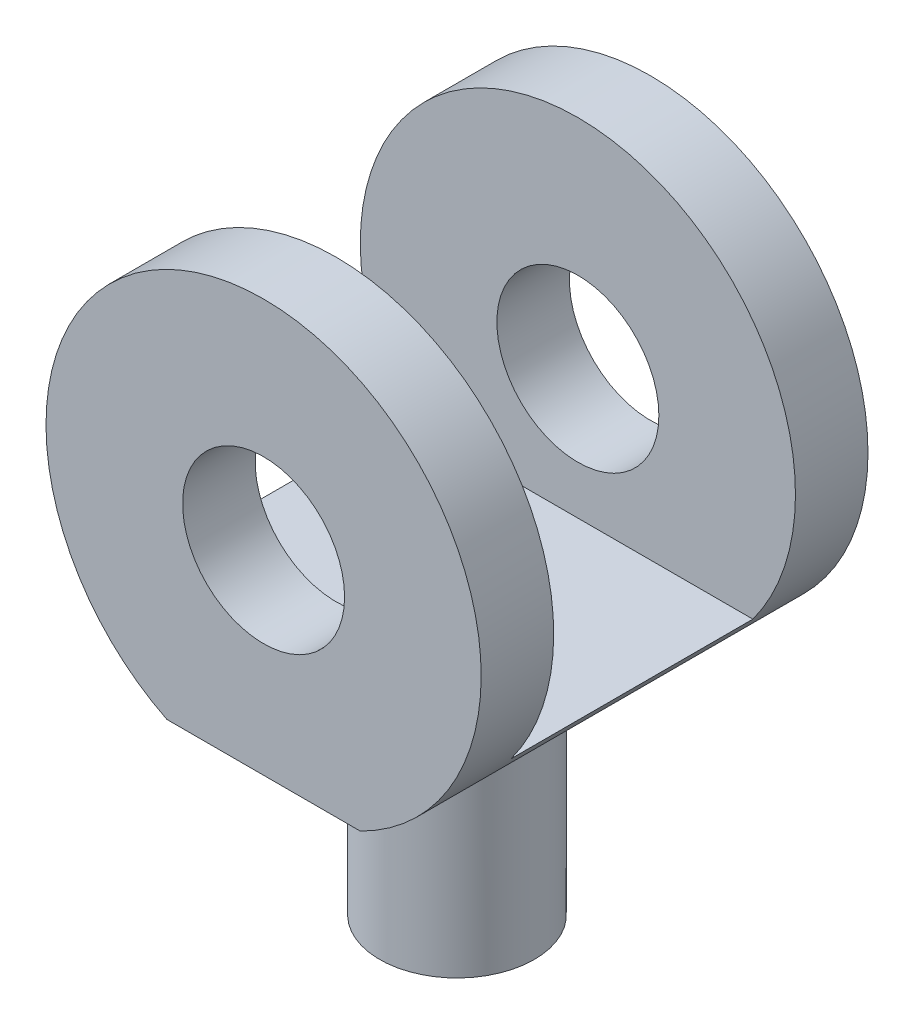
SolidWorks part; units mm, degrees
ref_plane "Front" through (0, 0, 0) normal (0, 0, 1) x (1, 0, 0)
ref_plane "Top" through (0, 0, 0) normal (0, 1, 0) x (1, 0, 0)
ref_plane "Right" through (0, 0, 0) normal (1, 0, 0) x (0, 0, -1)
sketch "Sketch1" plane through (0, 0, 0) normal (0, 0, 1) x (1, 0, 0)
  line L0 (13, -4.0311) -> (17, -4.0311)
  circle A0 centre (15, 0) radius 1.675 construction
  circle A1 centre (15, 0) radius 1.675
  arc A2 (17, -4.0311) -> (13, -4.0311) centre (15, 0) ccw
  point P8 (16.4351, 2.2425)
  point P9 (13.6936, -2.1573)
  dimension "D2" = 4.5
  dimension "D1" = 4
extrude "Boss-Extrude1" add sketch "Sketch1" along normal mid plane 8
sketch "Sketch2" plane through (0, 0, 0) normal (0, 0, 1) x (1, 0, 0)
  line L0 (-15, -2.675) -> (15, -2.675) construction
  line L1 (11.3814, -2.675) -> (18.6186, -2.675)
  arc A4 (17, -4.0311) -> (13, -4.0311) centre (15, 0) ccw construction
  arc A5 (18.6186, -2.675) -> (11.3814, -2.675) centre (15, 0) ccw
  point P6 (26.7814, 10.4658)
  point P7 (18.6186, -2.675)
extrude "Cut-Extrude1" cut sketch "Sketch2" against normal mid plane 5
sketch "Sketch3" plane through (0, -4.0311, 0) normal (0, -1, 0) x (1, 0, 0)
  line L0 (13, 4) -> (17, 4) construction
  line L1 (15, 4) -> (15, -5.8845) construction
  circle A0 centre (15, 0) radius 1.6
  point P2 (0, 0)
  dimension "D1" = 3.2
extrude "Boss-Extrude2" add sketch "Sketch3" along normal blind 4.5
fillet "Fillet1" radius 0.5 1 edges at (15, -4.0311, 1.6)
